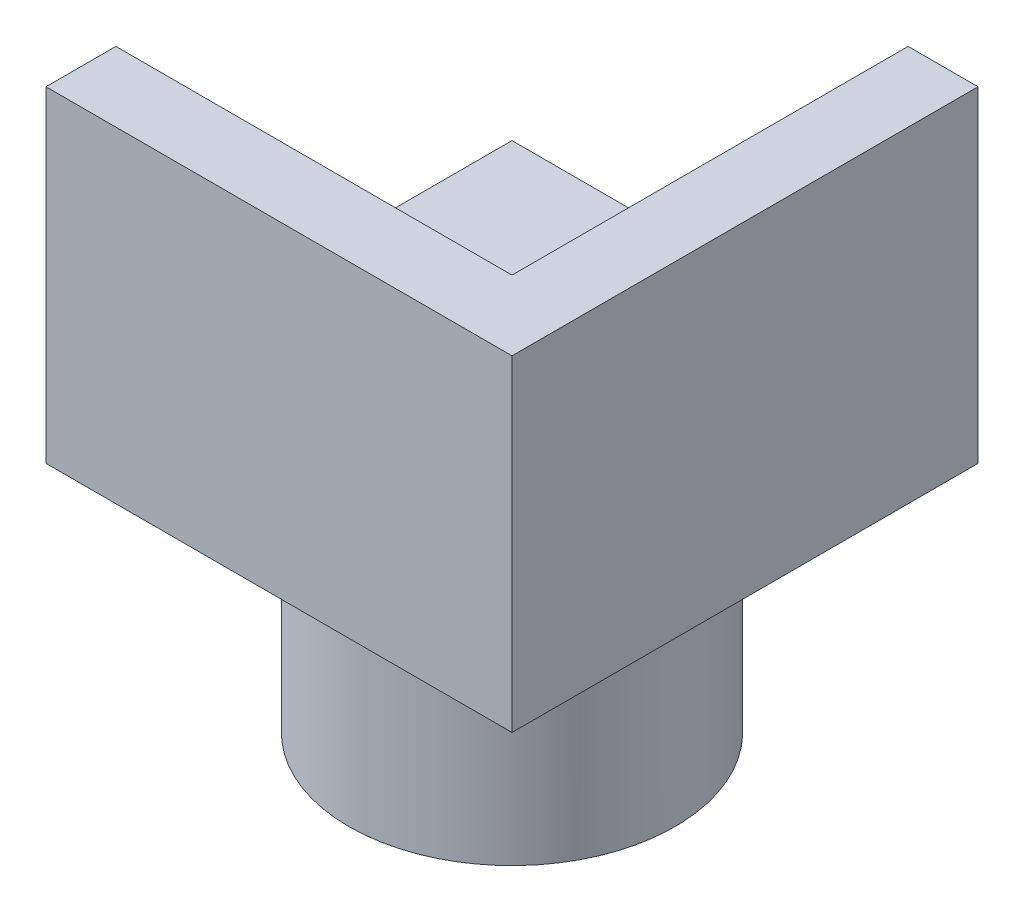
SolidWorks part; units mm, degrees
ref_plane "Front Plane" through (0, 0, 0) normal (0, 0, 1) x (1, 0, 0)
ref_plane "Top Plane" through (0, 0, 0) normal (0, 1, 0) x (1, 0, 0)
ref_plane "Right Plane" through (0, 0, 0) normal (1, 0, 0) x (0, 0, -1)
sketch "Sketch1" plane through (0, 0, 0) normal (0, 1, 0) x (1, 0, 0)
  line L0 (5, 5) -> (-5, -5) construction
  line L1 (-5, 5) -> (5, 5)
  line L2 (-5, 5) -> (-5, -5)
  line L3 (-5, -5) -> (5, -5)
  line L4 (5, 5) -> (5, -5)
  line L5 (5, -5) -> (-5, 5) construction
  point P0 (0, 0)
  dimension "D1" = 10
  dimension "D2" = 10
extrude "Boss-Extrude1" add sketch "Sketch1" along normal blind 1
sketch "Sketch2" plane through (0, 1, 0) normal (0, 1, 0) x (1, 0, 0)
  line L0 (0, 0.5) -> (0, -0.5) construction
  line L1 (2.5, 0.5) -> (2.5, -0.5)
  line L2 (-2.5, 0.5) -> (-2.5, -0.5)
  arc A0 (2.5, 0.5) -> (-2.5, 0.5) centre (0, 0.5) ccw
  arc A1 (-2.5, -0.5) -> (2.5, -0.5) centre (0, -0.5) ccw
  point P2 (0, 0)
  point P7 (0, 3)
  point P8 (0, -3)
  dimension "D1" = 5
  dimension "D2" = 6
extrude "Cut-Extrude1" cut sketch "Sketch2" against normal blind 1.5
sketch "Sketch3" plane through (0, 0, 0) normal (0, -1, 0) x (1, 0, 0)
  circle A3 centre (0, 0) radius 3.5
  dimension "D1" = 7
extrude "Boss-Extrude2" add sketch "Sketch3" along normal blind 5
sketch "Sketch4" plane through (0, 0, 0) normal (0, 1, 0) x (1, 0, 0)
  circle A0 centre (0, 0) radius 2
  dimension "D1" = 4
extrude "Cut-Extrude2" cut sketch "Sketch4" against normal through all
sketch "Sketch6" plane through (0, 1, 0) normal (0, 1, 0) x (1, 0, 0)
  line L0 (3.5, 3.5) -> (3.5, 5)
  line L1 (-5, -3.5) -> (-5, -5)
  line L2 (-5, -3.5) -> (5, -3.5)
  line L3 (5, -5) -> (5, 5) construction
  line L4 (5, 5) -> (-5, 5) construction
  line L5 (3.5, -5) -> (3.5, 3.5)
  line L6 (3.5, 3.5) -> (-5, 3.5)
  line L7 (3.5, -3.5) -> (3.5, 3.5)
  line L9 (5, -5) -> (5, 5)
  line L10 (5, 5) -> (3.5, 5)
  line L13 (-5, -3.5) -> (3.5, -3.5)
  line L15 (5, -5) -> (-5, -5)
  dimension "D1" = 1.5
  dimension "D2" = 1.5
extrude "Boss-Extrude3" add sketch "Sketch6" along normal blind 6
